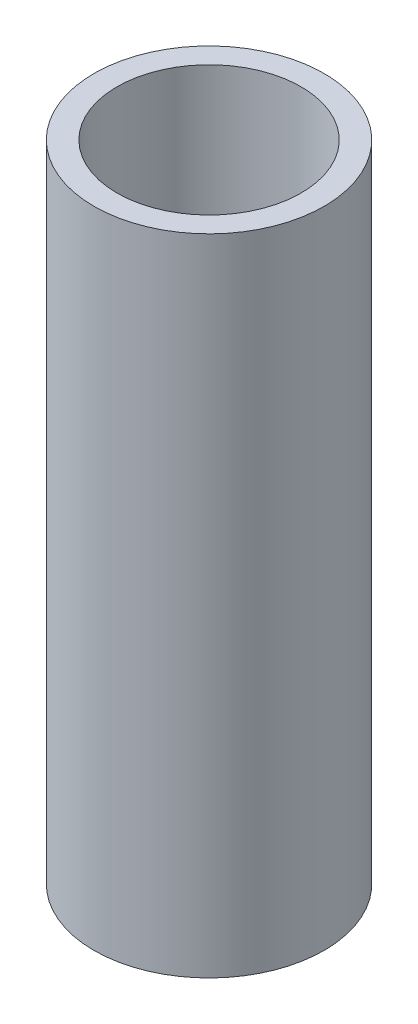
SolidWorks part; units mm, degrees
ref_plane "Alzado" through (0, 0, 0) normal (0, 0, 1) x (1, 0, 0)
ref_plane "Planta" through (0, 0, 0) normal (0, 1, 0) x (1, 0, 0)
ref_plane "Vista lateral" through (0, 0, 0) normal (1, 0, 0) x (0, 0, -1)
sketch "Croquis1" plane through (0, 0, 0) normal (0, 1, 0) x (1, 0, 0)
  circle A0 centre (0, 0) radius 12.5
  circle A1 centre (0, 0) radius 10
  dimension "D1" = 25
  dimension "D2" = 20
extrude "Saliente-Extruir1" add sketch "Croquis1" along normal mid plane 70
